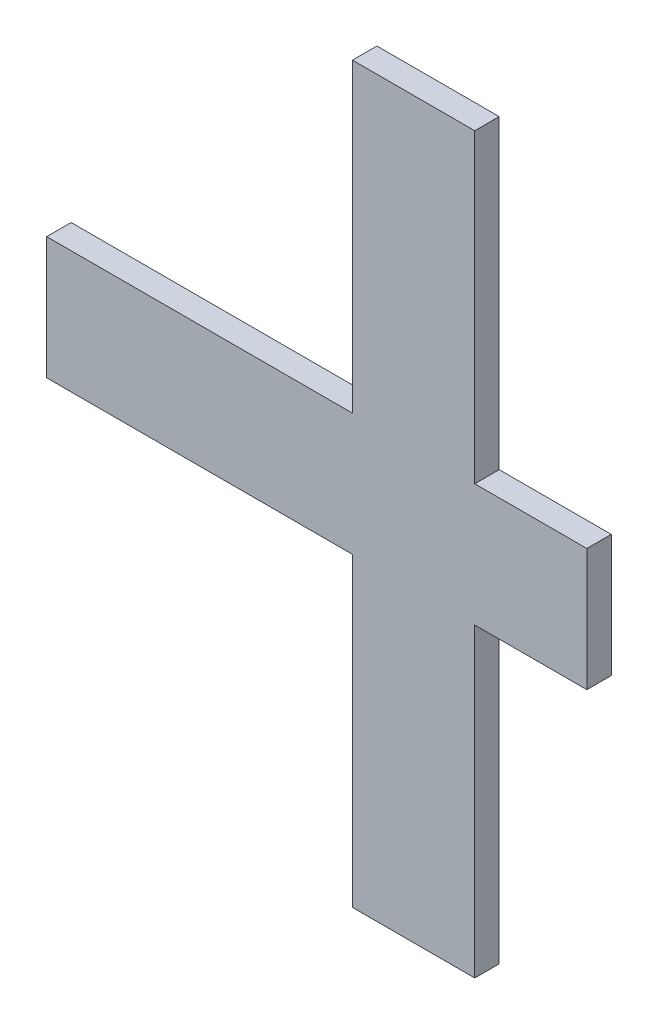
SolidWorks part; units mm, degrees
ref_plane "Plano frontal" through (0, 0, 0) normal (0, 0, 1) x (1, 0, 0)
ref_plane "Plano superior" through (0, 0, 0) normal (0, 1, 0) x (1, 0, 0)
ref_plane "Plano direito" through (0, 0, 0) normal (1, 0, 0) x (0, 0, -1)
sketch "Esboço1" plane through (0, 0, 0) normal (0, 0, 1) x (1, 0, 0)
  line L0 (0, 90) -> (184.1326, 90) construction
  line L1 (0, 0) -> (105, 0)
  line L2 (0, 0) -> (0, 180)
  line L3 (0, 180) -> (105, 180)
  line L4 (105, 0) -> (105, 180)
  line L5 (0, 180) -> (75, 180)
  line L6 (0, 180) -> (0, 105)
  line L7 (0, 105) -> (75, 105)
  line L8 (75, 180) -> (75, 105)
  line L9 (0, 0) -> (75, 0)
  line L10 (0, 0) -> (0, 75)
  line L11 (0, 75) -> (75, 75)
  line L12 (75, 0) -> (75, 75)
  line L13 (75, 180) -> (90, 180)
  line L14 (90, 180) -> (90, 0) construction
  line L15 (90, 90) -> (132.5, 90) construction
  line L16 (132.5, 90) -> (132.5, 105) construction
  line L18 (132.5, 105) -> (105, 105)
  line L19 (132.5, 105) -> (132.5, 75)
  line L20 (132.5, 75) -> (105, 75)
  line L21 (105, 105) -> (105, 75)
  dimension "D1" = 180
  dimension "D2" = 105
  dimension "D3" = 75
  dimension "D4" = 75
  dimension "D5" = 15
  dimension "D6" = 42.5
extrude "Ressalto-extrusão1" add sketch "Esboço1" along normal blind 6 contours L12 L1 L4 L3 L8 L7 L2 L11 | L20 L19 L18 L4
